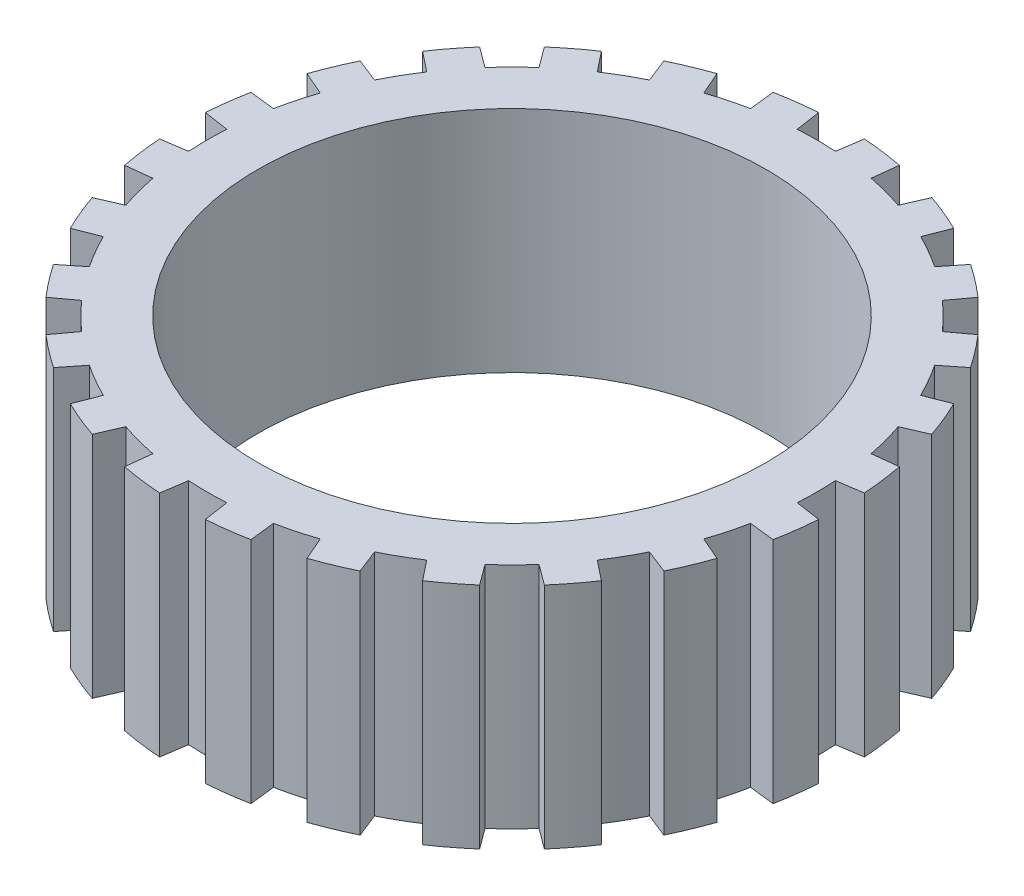
SolidWorks part; units mm, degrees
ref_plane "Front Plane" through (0, 0, 0) normal (0, 0, 1) x (1, 0, 0)
ref_plane "Top Plane" through (0, 0, 0) normal (0, 1, 0) x (1, 0, 0)
ref_plane "Right Plane" through (0, 0, 0) normal (1, 0, 0) x (0, 0, -1)
sketch "Sketch2" plane through (0, 0, 0) normal (0, 0, 1) x (1, 0, 0)
  line L0 (50, 0) -> (60, 0)
  line L2 (33, 0) -> (-33, 0) construction
  line L3 (60, 0) -> (60, 45)
  line L4 (60, 45) -> (50, 45)
  line L5 (50, 45) -> (50, 0)
  line L7 (0, -1000) -> (0, 49000) construction
  point P12 (0, 0)
  dimension "D1" = 10
  dimension "D2" = 100
  dimension "D3" = 45
revolve "Revolve1" add sketch "Sketch2" angle 360 about L7
sketch "Sketch3" plane through (0, 0, 0) normal (0, 1, 0) x (1, 0, 0)
  line L0 (0, -1000) -> (0, 49000) construction
  line L1 (4.5023, 64.8439) -> (3.7608, 59.882)
  line L2 (11.866, 58.815) -> (12.4339, 63.7997)
  line L3 (8.3093, 84.3659) -> (-4892.5477, -49674.8704) construction
  line L4 (8.4842, 64.4439) -> (7.8316, 59.4867) construction
  line L5 (21.1318, 61.4691) -> (19.1312, 56.8682)
  line L6 (26.6841, 53.7397) -> (28.5228, 58.4076)
  line L7 (36.3211, 53.9053) -> (33.1979, 49.979)
  line L8 (39.6837, 45.0023) -> (42.6679, 49.0352)
  line L9 (49.0352, 42.6679) -> (45.0023, 39.6837)
  line L10 (49.979, 33.1979) -> (53.9053, 36.3211)
  line L11 (58.4076, 28.5228) -> (53.7397, 26.6841)
  line L12 (4.5023, 64.8439) -> (0, 60) construction
  line L13 (56.8682, 19.1312) -> (61.4691, 21.1318)
  line L14 (63.7997, 12.4339) -> (58.815, 11.866)
  line L15 (59.882, 3.7608) -> (64.8439, 4.5023)
  line L16 (60, 0) -> (64.8439, 4.5023) construction
  line L17 (64.8439, -4.5023) -> (59.882, -3.7608)
  line L18 (58.815, -11.866) -> (63.7997, -12.4339)
  line L19 (61.4691, -21.1318) -> (56.8682, -19.1312)
  line L20 (53.7397, -26.6841) -> (58.4076, -28.5228)
  line L21 (53.9053, -36.3211) -> (49.979, -33.1979)
  line L22 (45.0023, -39.6837) -> (49.0352, -42.6679)
  line L23 (42.6679, -49.0352) -> (39.6837, -45.0023)
  line L24 (33.1979, -49.979) -> (36.3211, -53.9053)
  line L25 (28.5228, -58.4076) -> (26.6841, -53.7397)
  line L26 (19.1312, -56.8682) -> (21.1318, -61.4691)
  line L27 (12.4339, -63.7997) -> (11.866, -58.815)
  line L28 (3.7608, -59.882) -> (4.5023, -64.8439)
  line L29 (-4.5023, -64.8439) -> (-3.7608, -59.882)
  line L30 (-11.866, -58.815) -> (-12.4339, -63.7997)
  line L31 (-21.1318, -61.4691) -> (-19.1312, -56.8682)
  line L32 (-26.6841, -53.7397) -> (-28.5228, -58.4076)
  line L33 (-36.3211, -53.9053) -> (-33.1979, -49.979)
  line L34 (-39.6837, -45.0023) -> (-42.6679, -49.0352)
  line L35 (-49.0352, -42.6679) -> (-45.0023, -39.6837)
  line L36 (-49.979, -33.1979) -> (-53.9053, -36.3211)
  line L37 (-58.4076, -28.5228) -> (-53.7397, -26.6841)
  line L38 (-56.8682, -19.1312) -> (-61.4691, -21.1318)
  line L39 (-63.7997, -12.4339) -> (-58.815, -11.866)
  line L40 (-59.882, -3.7608) -> (-64.8439, -4.5023)
  line L41 (-64.8439, 4.5023) -> (-59.882, 3.7608)
  line L42 (-58.815, 11.866) -> (-63.7997, 12.4339)
  line L43 (-61.4691, 21.1318) -> (-56.8682, 19.1312)
  line L44 (-53.7397, 26.6841) -> (-58.4076, 28.5228)
  line L45 (-53.9053, 36.3211) -> (-49.979, 33.1979)
  line L46 (-45.0023, 39.6837) -> (-49.0352, 42.6679)
  line L47 (-42.6679, 49.0352) -> (-39.6837, 45.0023)
  line L48 (-33.1979, 49.979) -> (-36.3211, 53.9053)
  line L49 (-28.5228, 58.4076) -> (-26.6841, 53.7397)
  line L50 (-19.1312, 56.8682) -> (-21.1318, 61.4691)
  line L51 (-12.4339, 63.7997) -> (-11.866, 58.815)
  line L52 (-3.7608, 59.882) -> (-4.5023, 64.8439)
  line L53 (-4.5023, 64.8439) -> (4.5023, 64.8439) construction
  line L54 (12.4339, 63.7997) -> (21.1318, 61.4691) construction
  line L55 (0, 60) -> (-4.5023, 64.8439) construction
  circle A0 centre (0, 0) radius 60 construction
  arc A1 (4.5023, 64.8439) -> (12.4339, 63.7997) centre (0, 0) cw
  arc A2 (3.7608, 59.882) -> (11.866, 58.815) centre (0, 0) cw
  arc A3 (19.1312, 56.8682) -> (26.6841, 53.7397) centre (0, 0) cw
  arc A4 (21.1318, 61.4691) -> (28.5228, 58.4076) centre (0, 0) cw
  arc A5 (33.1979, 49.979) -> (39.6837, 45.0023) centre (0, 0) cw
  arc A6 (36.3211, 53.9053) -> (42.6679, 49.0352) centre (0, 0) cw
  arc A7 (45.0023, 39.6837) -> (49.979, 33.1979) centre (0, 0) cw
  arc A8 (49.0352, 42.6679) -> (53.9053, 36.3211) centre (0, 0) cw
  arc A9 (53.7397, 26.6841) -> (56.8682, 19.1312) centre (0, 0) cw
  arc A10 (58.4076, 28.5228) -> (61.4691, 21.1318) centre (0, 0) cw
  arc A11 (58.815, 11.866) -> (59.882, 3.7608) centre (0, 0) cw
  arc A12 (63.7997, 12.4339) -> (64.8439, 4.5023) centre (0, 0) cw
  arc A13 (59.882, -3.7608) -> (58.815, -11.866) centre (0, 0) cw
  arc A14 (64.8439, -4.5023) -> (63.7997, -12.4339) centre (0, 0) cw
  arc A15 (56.8682, -19.1312) -> (53.7397, -26.6841) centre (0, 0) cw
  arc A16 (61.4691, -21.1318) -> (58.4076, -28.5228) centre (0, 0) cw
  arc A17 (49.979, -33.1979) -> (45.0023, -39.6837) centre (0, 0) cw
  arc A18 (53.9053, -36.3211) -> (49.0352, -42.6679) centre (0, 0) cw
  arc A19 (39.6837, -45.0023) -> (33.1979, -49.979) centre (0, 0) cw
  arc A20 (42.6679, -49.0352) -> (36.3211, -53.9053) centre (0, 0) cw
  arc A21 (26.6841, -53.7397) -> (19.1312, -56.8682) centre (0, 0) cw
  arc A22 (28.5228, -58.4076) -> (21.1318, -61.4691) centre (0, 0) cw
  arc A23 (11.866, -58.815) -> (3.7608, -59.882) centre (0, 0) cw
  arc A24 (12.4339, -63.7997) -> (4.5023, -64.8439) centre (0, 0) cw
  arc A25 (-3.7608, -59.882) -> (-11.866, -58.815) centre (0, 0) cw
  arc A26 (-4.5023, -64.8439) -> (-12.4339, -63.7997) centre (0, 0) cw
  arc A27 (-19.1312, -56.8682) -> (-26.6841, -53.7397) centre (0, 0) cw
  arc A28 (-21.1318, -61.4691) -> (-28.5228, -58.4076) centre (0, 0) cw
  arc A29 (-33.1979, -49.979) -> (-39.6837, -45.0023) centre (0, 0) cw
  arc A30 (-36.3211, -53.9053) -> (-42.6679, -49.0352) centre (0, 0) cw
  arc A31 (-45.0023, -39.6837) -> (-49.979, -33.1979) centre (0, 0) cw
  arc A32 (-49.0352, -42.6679) -> (-53.9053, -36.3211) centre (0, 0) cw
  arc A33 (-53.7397, -26.6841) -> (-56.8682, -19.1312) centre (0, 0) cw
  arc A34 (-58.4076, -28.5228) -> (-61.4691, -21.1318) centre (0, 0) cw
  arc A35 (-58.815, -11.866) -> (-59.882, -3.7608) centre (0, 0) cw
  arc A36 (-63.7997, -12.4339) -> (-64.8439, -4.5023) centre (0, 0) cw
  arc A37 (-59.882, 3.7608) -> (-58.815, 11.866) centre (0, 0) cw
  arc A38 (-64.8439, 4.5023) -> (-63.7997, 12.4339) centre (0, 0) cw
  arc A39 (-56.8682, 19.1312) -> (-53.7397, 26.6841) centre (0, 0) cw
  arc A40 (-61.4691, 21.1318) -> (-58.4076, 28.5228) centre (0, 0) cw
  arc A41 (-49.979, 33.1979) -> (-45.0023, 39.6837) centre (0, 0) cw
  arc A42 (-53.9053, 36.3211) -> (-49.0352, 42.6679) centre (0, 0) cw
  arc A43 (-39.6837, 45.0023) -> (-33.1979, 49.979) centre (0, 0) cw
  arc A44 (-42.6679, 49.0352) -> (-36.3211, 53.9053) centre (0, 0) cw
  arc A45 (-26.6841, 53.7397) -> (-19.1312, 56.8682) centre (0, 0) cw
  arc A46 (-28.5228, 58.4076) -> (-21.1318, 61.4691) centre (0, 0) cw
  arc A47 (-11.866, 58.815) -> (-3.7608, 59.882) centre (0, 0) cw
  arc A48 (-12.4339, 63.7997) -> (-4.5023, 64.8439) centre (0, 0) cw
  point P28 (0, 0)
  point P111 (0, 0)
  dimension "D1" = 120
  dimension "D2" = 5
  dimension "D4" = 5.625
  dimension "D5" = 6
  dimension "D6" = 8
  dimension "D3" = 2
  dimension "D8" = 4
extrude "Boss-Extrude1" add sketch "Sketch3" along normal blind 45
